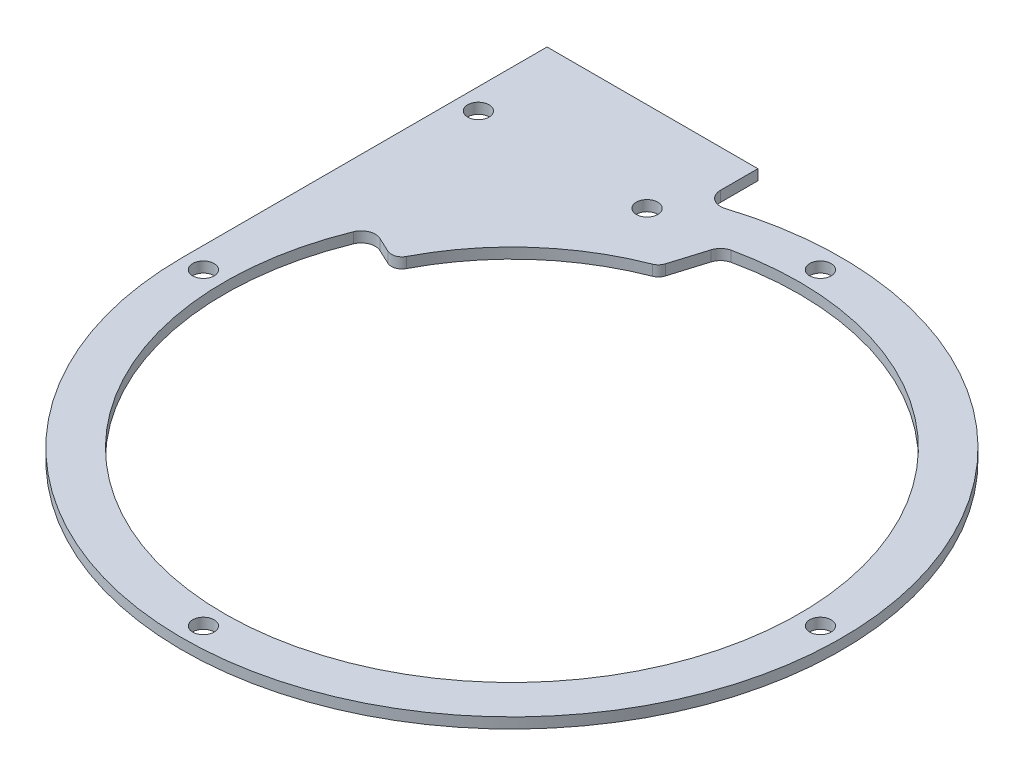
SolidWorks part; units mm, degrees
material "Thornel Mat VMA"
ref_plane "前视基准面" through (0, 0, 0) normal (0, 0, 1) x (1, 0, 0)
ref_plane "上视基准面" through (0, 0, 0) normal (0, 1, 0) x (1, 0, 0)
ref_plane "右视基准面" through (0, 0, 0) normal (1, 0, 0) x (0, 0, -1)
sketch "草图1" plane through (0, 0, 0) normal (0, 1, 0) x (1, 0, 0)
  line L0 (-46.9, 0) -> (-46.9, 46.9)
  line L1 (-46.9, 46.9) -> (-16.9, 46.9)
  line L2 (-16.9, 46.9) -> (-16.9, 46.5747)
  line L3 (-31.9, 0) -> (-31.9, 46.9) construction
  line L4 (-19.9, 46.9) -> (-19.9, 39.1306) construction
  line L5 (-19.9, 46.9) -> (-19.9, 43.7493) construction
  line L6 (-43.9, 0) -> (-43.9, 46.9) construction
  line L7 (-16.9, 46.9) -> (-16.9, 43.7493) construction
  arc A0 (-46.9, 0) -> (-14.2906, 44.6698) centre (0, 0) ccw
  circle A1 centre (0, 0) radius 40.9
  circle A2 centre (0, 0) radius 31.9 construction
  circle A4 centre (0, 0) radius 43.9 construction
  circle A5 centre (-19.9, 39.1306) radius 1.525
  circle A6 centre (0, 43.9) radius 1.525
  circle A7 centre (43.9, 0) radius 1.525
  circle A8 centre (0, -43.9) radius 1.525
  circle A9 centre (-43.9, 0) radius 1.525
  circle A20 centre (0, 0) radius 46.9 construction
  circle A21 centre (-43.9, 39.1306) radius 1.525
  arc A22 (-16.9, 46.5747) -> (-14.2906, 44.6698) centre (-14.9, 46.5747) ccw
  dimension "D1" = 93.8
  dimension "D8" = 3.05
  dimension "D4" = 2
  dimension "D2" = 6
  dimension "D3" = 9
  dimension "D5" = 3
  dimension "D6" = 3
  dimension "D7" = 4
extrude "凸台-拉伸1" add sketch "草图1" along normal blind 1.5
sketch "草图2" plane through (0, 0, 0) normal (0, 1, 0) x (1, 0, 0)
  line L0 (0, 0) -> (-37.068, 17.2851) construction
  line L1 (-37.068, 17.2851) -> (-33.0523, 15.4125)
  line L2 (0, 0) -> (-43.9, 0) construction
  line L3 (0, 0) -> (-11.9707, 32.8892) construction
  line L4 (0, 0) -> (-9.8946, 39.6851) construction
  line L5 (-11.755, 33.5954) -> (-9.8946, 39.6851)
  arc A0 (-12.6475, 32.635) -> (-31.0861, 16.0827) centre (0, 0) ccw
  arc A1 (-9.8946, 39.6851) -> (-37.068, 17.2851) centre (0, 0) ccw
  circle A2 centre (0, 0) radius 40.9 construction
  arc A3 (-12.6475, 32.635) -> (-11.755, 33.5954) centre (-13.1895, 34.0336) ccw
  arc A4 (-33.0523, 15.4125) -> (-31.0861, 16.0827) centre (-32.4184, 16.772) ccw
  point P16 (-31.7208, 14.7916)
  dimension "D1" = 70
  dimension "D4" = 1.5
  dimension "D2" = 45
  dimension "D3" = 6
  dimension "D5" = 25
extrude "凸台-拉伸3" add sketch "草图2" along normal up to surface (1.5 mm away) up to face at (-43.9, 1.5, 1.525)
fillet "圆角1" radius 2 2 edges at (-9.8946, 0.75, -39.6851) (-37.068, 0.75, -17.2851)
sketch "草图3" plane through (0, 1.5, 0) normal (0, 1, 0) x (1, 0, 0)
  line L1 (-46.9, 46.9) -> (-16.9, 46.9)
  line L2 (-46.9, 46.9) -> (-46.9, 51.9)
  line L3 (-46.9, 51.9) -> (-16.9, 51.9)
  line L4 (-16.9, 46.9) -> (-16.9, 51.9)
  dimension "D1" = 5
extrude "凸台-拉伸4" add sketch "草图3" against normal blind 1.5
